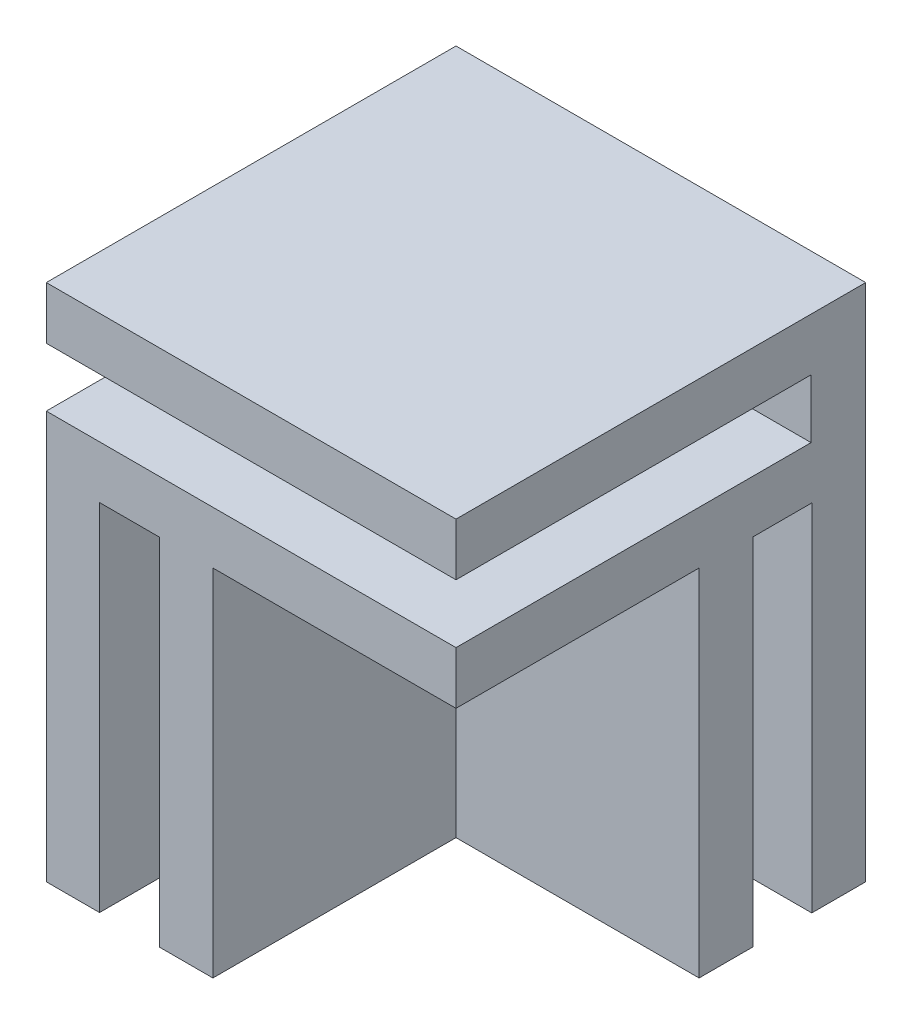
SolidWorks part; units mm, degrees
ref_plane "Plan de face" through (0, 0, 0) normal (0, 0, 1) x (1, 0, 0)
ref_plane "Plan de dessus" through (0, 0, 0) normal (0, 1, 0) x (1, 0, 0)
ref_plane "Plan de droite" through (0, 0, 0) normal (1, 0, 0) x (0, 0, -1)
sketch "Esquisse1" plane through (0, 0, 0) normal (0, 1, 0) x (1, 0, 0)
  line L1 (-35.8867, 13.5315) -> (-5.8867, 13.5315)
  line L2 (-35.8867, 13.5315) -> (-35.8867, -16.4685)
  line L3 (-35.8867, -16.4685) -> (-5.8867, -16.4685)
  line L4 (-5.8867, 13.5315) -> (-5.8867, -16.4685)
  dimension "D1" = 30
  dimension "D2" = 30
extrude "Boss.-Extru.1" add sketch "Esquisse1" along normal blind 38
sketch "Esquisse2" plane through (0, 0, 0) normal (0, -1, 0) x (1, 0, 0)
  line L0 (-5.8867, 16.4685) -> (-5.8867, -13.5315) construction
  line L1 (-5.8867, -9.5815) -> (-23.6867, -9.5815)
  line L2 (-5.8867, -9.5815) -> (-5.8867, -5.2815)
  line L3 (-5.8867, -5.2815) -> (-23.6867, -5.2815)
  line L4 (-23.6867, -9.5815) -> (-23.6867, -5.2815)
  line L5 (-35.8867, 16.4685) -> (-5.8867, 16.4685) construction
  line L6 (-27.5867, 16.4685) -> (-31.9867, 16.4685)
  line L7 (-27.5867, 16.4685) -> (-27.5867, -1.3315)
  line L8 (-27.5867, -1.3315) -> (-31.9867, -1.3315)
  line L9 (-31.9867, 16.4685) -> (-31.9867, -1.3315)
  line L15 (-35.8867, -13.5315) -> (-35.8867, 16.4685) construction
  line L16 (-5.8867, -13.5315) -> (-35.8867, -13.5315) construction
  line L18 (-5.8867, 16.4685) -> (-23.6867, 16.4685)
  line L19 (-5.8867, 16.4685) -> (-5.8867, -1.3315)
  line L20 (-5.8867, -1.3315) -> (-23.6867, -1.3315)
  line L21 (-23.6867, 16.4685) -> (-23.6867, -1.3315)
  dimension "D1" = 4.4
  dimension "D2" = 17.8
  dimension "D3" = 3.9
  dimension "D4" = 4.3
  dimension "D5" = 17.8
  dimension "D6" = 3.95
  dimension "D7" = 3.95
  dimension "D8" = 3.9
extrude "Enlèv. mat.-Extru.1" cut sketch "Esquisse2" against normal blind 26
sketch "Esquisse5" plane through (-35.8867, 0, 0) normal (-1, 0, 0) x (0, 0, 1)
  line L0 (16.4685, 38) -> (16.4685, 0) construction
  line L1 (16.4685, 34.15) -> (-9.5315, 34.15)
  line L2 (16.4685, 34.15) -> (16.4685, 29.85)
  line L3 (16.4685, 29.85) -> (-9.5315, 29.85)
  line L4 (-9.5315, 34.15) -> (-9.5315, 29.85)
  line L5 (-13.5315, 38) -> (-13.5315, 0) construction
  line L6 (-13.5315, 38) -> (16.4685, 38) construction
  dimension "D1" = 4
  dimension "D2" = 4.3
  dimension "D3" = 3.85
extrude "Enlèv. mat.-Extru.4" cut sketch "Esquisse5" against normal through all
